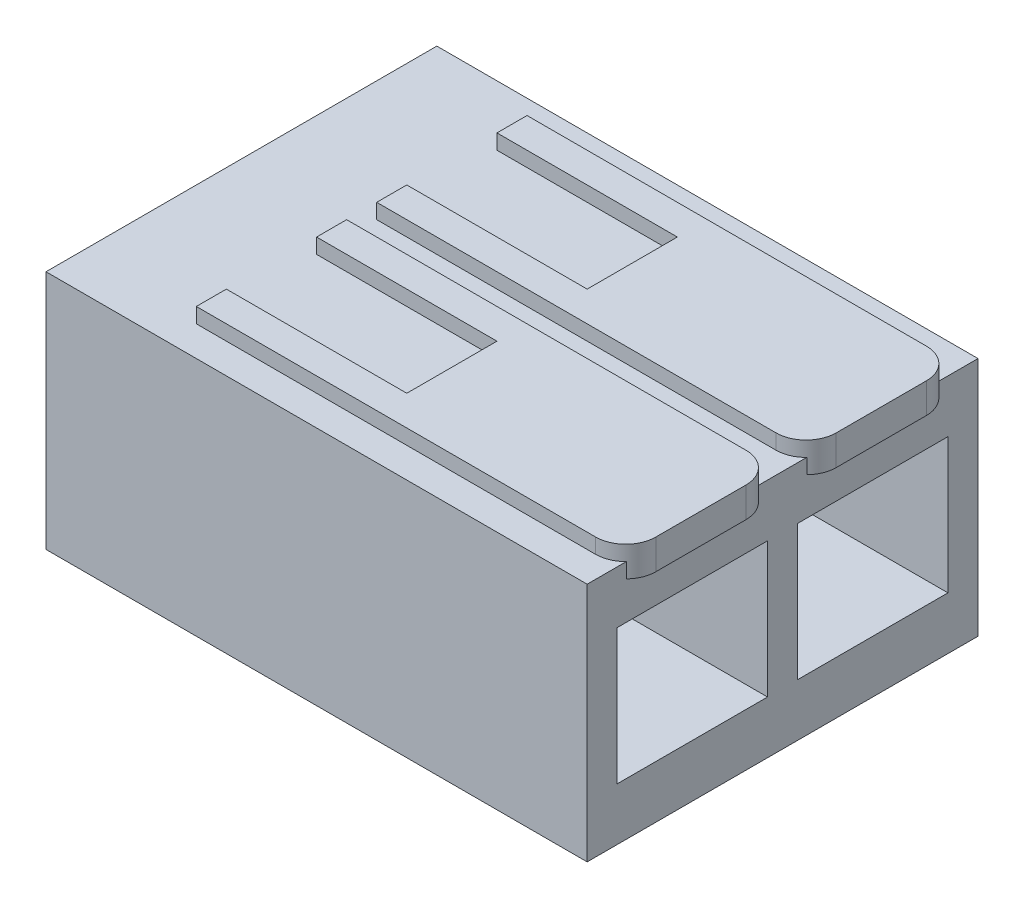
SolidWorks part; units mm, degrees
other "Objet de détail2"
material "Nylon 6/10"
ref_plane "Plan de face" through (0, 0, 0) normal (0, 0, 1) x (1, 0, 0)
ref_plane "Plan de dessus" through (0, 0, 0) normal (0, 1, 0) x (1, 0, 0)
ref_plane "Plan de droite" through (0, 0, 0) normal (1, 0, 0) x (0, 0, -1)
sketch "Esquisse1" plane through (0, 0, 0) normal (0, 0, 1) x (1, 0, 0)
  line L0 (0, 0) -> (18, 0)
  line L3 (18, 0) -> (18, 8)
  line L4 (18, 8) -> (0, 8)
  line L5 (0, 8) -> (0, 0) construction
  line L6 (0, 0) -> (0, 4)
  line L9 (0, 4) -> (0, 8)
  dimension "D1" = 18
  dimension "D3" = 8
extrude "Boss.-Extru.1" add sketch "Esquisse1" along normal blind 13
sketch "Esquisse4" plane through (18, 0, 0) normal (1, 0, 0) x (0, 0, -1)
  line L0 (-7, 4) -> (-6, 4) construction
  line L2 (-6, 6.25) -> (-1, 6.25)
  line L3 (-6, 6.25) -> (-6, 1.75)
  line L5 (-6, 1.75) -> (-1, 1.75)
  line L6 (-1, 6.25) -> (-1, 1.75)
  line L7 (-12, 6.25) -> (-7, 6.25)
  line L8 (-12, 6.25) -> (-12, 1.75)
  line L9 (-12, 1.75) -> (-7, 1.75)
  line L10 (-7, 6.25) -> (-7, 1.75)
  line L11 (-1, 4) -> (0, 4) construction
  line L12 (0, 0) -> (0, 8) construction
  dimension "D2" = 4.5
  dimension "D1" = 5
  dimension "D3" = 1
extrude "Enlèv. mat.-Extru.2" cut sketch "Esquisse4" against normal blind 5
sketch "Esquisse5" plane through (0, 8, 0) normal (0, 1, 0) x (1, 0, 0)
  line L0 (18.2832, -5) -> (18.2832, -8) construction
  line L1 (4, -1) -> (17.2832, -1)
  line L2 (4, -1) -> (4, -2)
  line L3 (4, -6) -> (17.2832, -6)
  line L4 (18.2832, -2) -> (18.2832, -5)
  line L5 (4, -7) -> (17.2832, -7)
  line L6 (4, -7) -> (4, -8)
  line L7 (4, -12) -> (17.2832, -12)
  line L8 (18.2832, -8) -> (18.2832, -11)
  line L9 (4, -6) -> (4, -7) construction
  line L10 (4, -7) -> (4.0355, -6.9823) construction
  line L11 (0, -13) -> (0, 0) construction
  line L13 (18, -13) -> (18, 0) construction
  line L14 (4, -2) -> (10, -2)
  line L15 (10, -2) -> (10, -5)
  line L16 (10, -5) -> (4, -5)
  line L17 (4, -8) -> (10, -8)
  line L18 (10, -8) -> (10, -11)
  line L19 (10, -11) -> (4, -11)
  line L20 (4, -5) -> (4, -6)
  line L21 (4, -11) -> (4, -12)
  line L22 (10, -8) -> (10, -5) construction
  arc A0 (17.2832, -12) -> (18.2832, -11) centre (17.2832, -11) ccw
  arc A1 (17.2832, -7) -> (18.2832, -8) centre (17.2832, -8) cw
  arc A2 (17.2832, -6) -> (18.2832, -5) centre (17.2832, -5) ccw
  arc A3 (17.2832, -1) -> (18.2832, -2) centre (17.2832, -2) cw
  dimension "D1" = 1
  dimension "D2" = 4
  dimension "D3" = 6
  dimension "D4" = 0.2832
extrude "Boss.-Extru.2" add sketch "Esquisse5" along normal mid plane 1 separate body
pattern_linear "Répétition linéaire1" [suppressed] count 2 spacing 4
equation "\"Cout_variable\"= int((\"Masse\" * \"Prix_au_kg\" + \"Prix_unitaire\" + \"Prix_m2\" * \"SW-Superficie\" / 1000000 + \"Prix_m3\" * \"SW-Volume\" /1000000)*100)/100"
equation "\"Cout_horaire\"= int((\"Taux_horaire_brut\" * \"Temps_fabrication\"  +  IIF ( \"Estimation_bois\" = 1 , \"SW-Volume\" * 350 /1000000,0))*100)/100"
